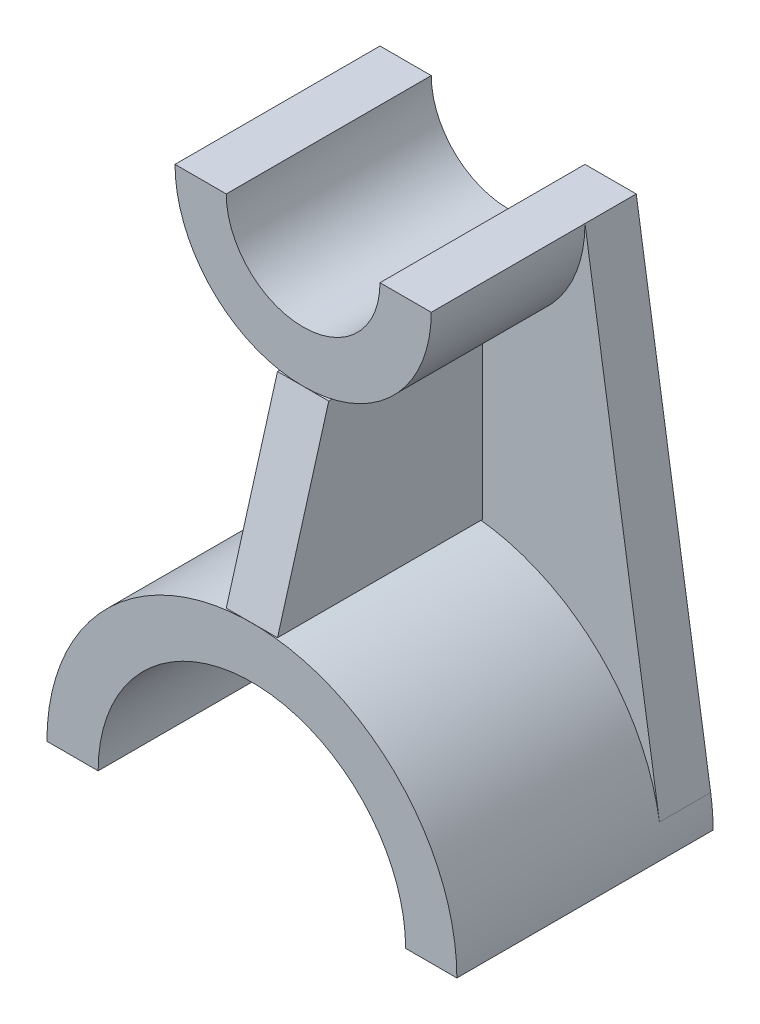
SolidWorks part; units mm, degrees
ref_plane "Front Plane" through (0, 0, 0) normal (0, 0, 1) x (1, 0, 0)
ref_plane "Top Plane" through (0, 0, 0) normal (0, 1, 0) x (1, 0, 0)
ref_plane "Right Plane" through (0, 0, 0) normal (1, 0, 0) x (0, 0, -1)
sketch "Sketch1" plane through (0, 0, 0) normal (0, 0, 1) x (1, 0, 0)
  line L0 (-40, 0) -> (-30, 0)
  line L1 (30, 0) -> (40, 0)
  arc A0 (-40, 0) -> (40, 0) centre (0, 0) cw
  arc A1 (-30, 0) -> (30, 0) centre (0, 0) cw
  dimension "D1" = 40
  dimension "D2" = 30
  dimension "D3" = 10
  dimension "D4" = 10
extrude "Boss-Extrude1" add sketch "Sketch1" along normal blind 50
sketch "Sketch2" plane through (0, 0, 0) normal (0, 0, 1) x (1, 0, 0)
  line L3 (-25, 100) -> (-15, 100)
  line L4 (15, 100) -> (25, 100)
  arc A1 (-25, 100) -> (25, 100) centre (0, 100) ccw
  arc A2 (-15, 100) -> (15, 100) centre (0, 100) ccw
  dimension "D2" = 25
  dimension "D3" = 15
  dimension "D1" = 100
extrude "Boss-Extrude4" add sketch "Sketch2" along normal blind 40 separate body
sketch "Sketch6" plane through (0, 0, 0) normal (0, 0, -1) x (-1, 0, 0)
  line L0 (-25, 100) -> (-39.5294, 6.1176)
  line L1 (25, 100) -> (39.5294, 6.1176)
  arc A0 (-25, 100) -> (25, 100) centre (0, 100) ccw construction
  arc A1 (40, 0) -> (-40, 0) centre (0, 0) ccw construction
  arc A2 (-25, 100) -> (25, 100) centre (0, 100) ccw
  arc A3 (39.5294, 6.1176) -> (-39.5294, 6.1176) centre (0, 0) ccw
extrude "Boss-Extrude6" add sketch "Sketch6" against normal blind 10
sketch "Sketch7" plane through (0, 0, 0) normal (1, 0, 0) x (0, 0, -1)
  line L0 (-40, 75) -> (-50, 40)
  line L1 (-40, 75) -> (-10, 75)
  line L2 (-10, 75) -> (-10, 40)
  line L3 (-10, 40) -> (-50, 40)
extrude "Boss-Extrude8" add sketch "Sketch7" along normal mid plane 10 separate body contours L0 L3 L2 L1
